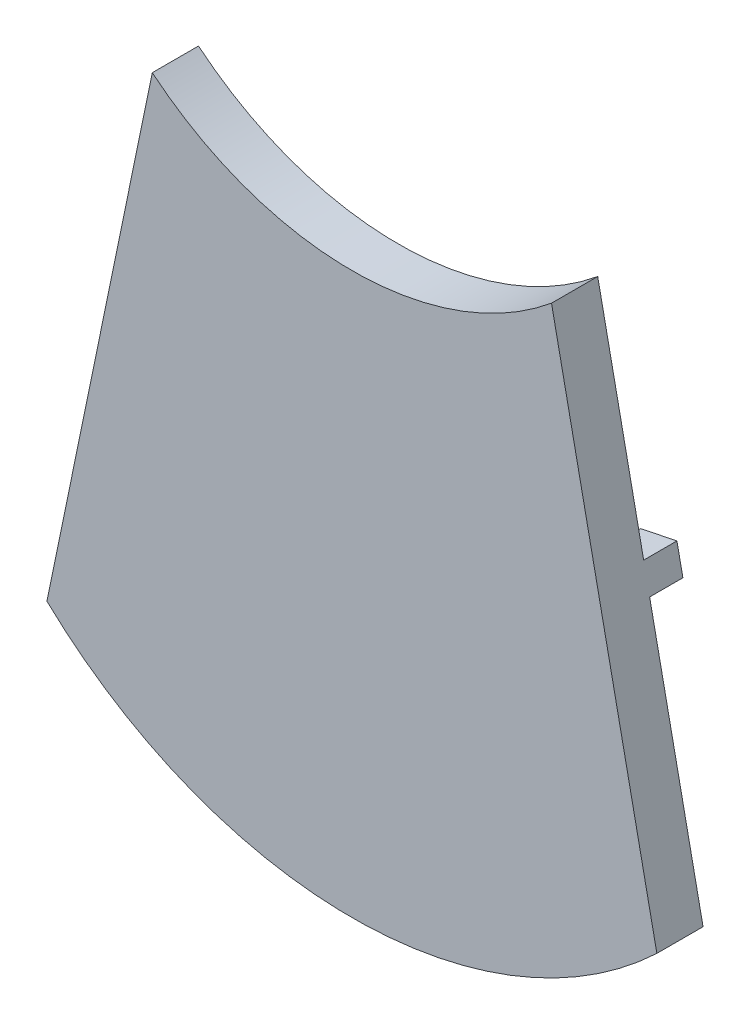
SolidWorks part; units mm, degrees
material "Oak"
ref_plane "Front Plane" through (0, 0, 0) normal (0, 0, 1) x (1, 0, 0)
ref_plane "Top Plane" through (0, 0, 0) normal (0, 1, 0) x (1, 0, 0)
ref_plane "Right Plane" through (0, 0, 0) normal (1, 0, 0) x (0, 0, -1)
sketch "Sketch1" plane through (0, 0, 0) normal (0, 0, 1) x (1, 0, 0)
  line L0 (0, 0) -> (36.195, 175.3738)
  line L1 (173.355, 175.3738) -> (209.55, 0)
  line L3 (104.775, 150.7904) -> (104.775, -41.7295) construction
  arc A2 (0, 0) -> (209.55, 0) centre (104.775, 110.6705) ccw
  arc A3 (36.195, 175.3738) -> (173.355, 175.3738) centre (104.775, 258.7404) ccw
  dimension "D5" = 107.95
  dimension "D3" = 209.55
  dimension "D4" = 152.4
  dimension "D1" = 137.16
  dimension "D2" = 179.07
extrude "Boss-Extrude1" add sketch "Sketch1" along normal blind 15.875
sketch "Sketch2" plane through (0, 0, 0) normal (0, 0, 1) x (1, 0, 0)
  line L0 (20.4078, 98.881) -> (39.0646, 95.0305)
  line L1 (36.195, 175.3738) -> (0, 0) construction
  line L2 (39.0646, 95.0305) -> (37.011, 85.0802)
  line L3 (37.011, 85.0802) -> (18.3542, 88.9307)
  line L4 (18.3542, 88.9307) -> (20.4078, 98.881)
  line L5 (189.1422, 98.881) -> (170.4854, 95.0305)
  line L6 (209.55, 0) -> (173.355, 175.3738) construction
  line L7 (170.4854, 95.0305) -> (172.539, 85.0802)
  line L8 (172.539, 85.0802) -> (191.1958, 88.9307)
  line L9 (191.1958, 88.9307) -> (189.1422, 98.881)
  line L10 (121.4477, -20.9931) -> (120.65, -14.6934)
  line L11 (120.65, -14.6934) -> (88.9, -14.6934)
  line L12 (88.9, -14.6934) -> (88.1023, -20.9931)
  line L13 (104.775, -22.0445) -> (104.775, -14.6934) construction
  arc A0 (121.4477, -20.9931) -> (88.1023, -20.9931) centre (104.775, 110.6705) cw
  arc A1 (0, 0) -> (209.55, 0) centre (104.775, 110.6705) ccw construction
  dimension "D5" = 132.715
  dimension "D1" = 10.16
  dimension "D2" = 78.105
  dimension "D3" = 19.05
  dimension "D4" = 19.05
  dimension "D6" = 6.35
  dimension "D7" = 31.75
extrude "Boss-Extrude2" add sketch "Sketch2" against normal blind 11.43
sketch "Sketch4" plane through (0, 0, 0) normal (0, 0, -1) x (-1, 0, 0)
  line L0 (-174.1373, 108.7518) -> (-181.325, 73.9258)
  line L1 (-28.225, 73.9258) -> (-35.4127, 108.7518)
  line L10 (-120.65, -14.6934) -> (-88.9, -14.6934) construction
  line L20 (-155.4805, 104.9013) -> (-162.6682, 70.0753)
  line L21 (-162.6682, 70.0753) -> (-181.325, 73.9258)
  line L22 (-181.325, 73.9258) -> (-195.6412, 4.5601)
  line L23 (-13.9088, 4.5601) -> (-28.225, 73.9258)
  line L24 (-28.225, 73.9258) -> (-46.8818, 70.0753)
  line L25 (-46.8818, 70.0753) -> (-54.0695, 104.9013)
  line L26 (-54.0695, 104.9013) -> (-35.4127, 108.7518)
  line L27 (-35.4127, 108.7518) -> (-44.7663, 154.0725)
  line L28 (-164.7837, 154.0725) -> (-174.1373, 108.7518)
  line L29 (-174.1373, 108.7518) -> (-155.4805, 104.9013)
  line L32 (-181.325, 73.9258) -> (-192.2709, 20.8899)
  line L33 (-17.2791, 20.8899) -> (-28.225, 73.9258)
  line L37 (-35.4127, 108.7518) -> (-44.7663, 154.0725)
  line L38 (-164.7837, 154.0725) -> (-174.1373, 108.7518)
  arc A2 (-192.2709, 20.8899) -> (-17.2791, 20.8899) centre (-104.775, 110.6705) ccw
  arc A3 (-209.55, 0) -> (0, 0) centre (-104.775, 110.6705) ccw construction
  arc A4 (-195.6412, 4.5601) -> (-13.9088, 4.5601) centre (-104.775, 110.6705) ccw
  arc A5 (-164.7837, 154.0725) -> (-44.7663, 154.0725) centre (-104.775, 258.7404) ccw
  arc A7 (-164.7837, 154.0725) -> (-44.7663, 154.0725) centre (-104.775, 258.7404) ccw
  dimension "D1" = 12.7
extrude "Cut-Extrude1" cut sketch "Sketch4" along normal through all and the other way blind 11.1125
